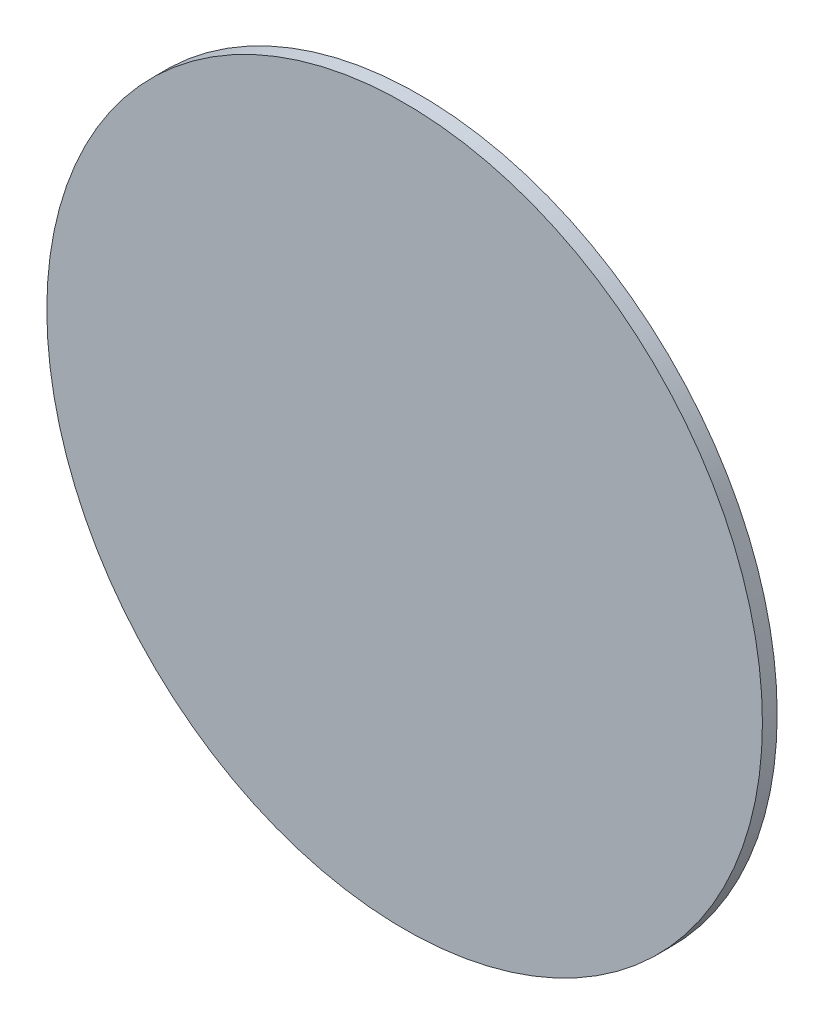
SolidWorks part; units mm, degrees
material "3.0205 (EN-AW 1200)"
ref_plane "Alzado" through (0, 0, 0) normal (0, 0, 1) x (1, 0, 0)
ref_plane "Planta" through (0, 0, 0) normal (0, 1, 0) x (1, 0, 0)
ref_plane "Vista lateral" through (0, 0, 0) normal (1, 0, 0) x (0, 0, -1)
sketch "Croquis1" plane through (0, 0, 0) normal (0, 0, 1) x (1, 0, 0)
  circle A0 centre (0, 0) radius 9.7
  dimension "D1" = 19.4
extrude "Saliente-Extruir1" add sketch "Croquis1" along normal blind 0.4
